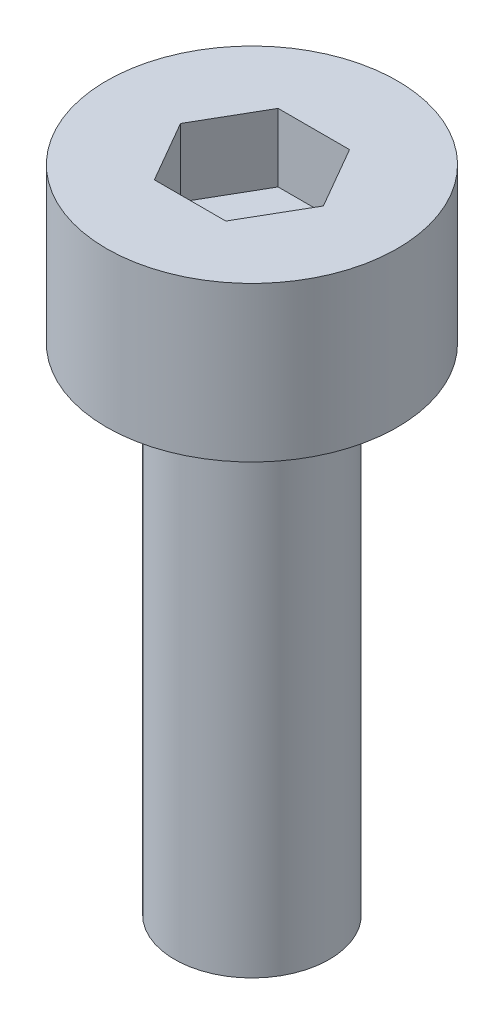
SolidWorks part; units mm, degrees
material "AISI 304"
ref_plane "前视基准面" through (0, 0, 0) normal (0, 0, 1) x (1, 0, 0)
ref_plane "上视基准面" through (0, 0, 0) normal (0, 1, 0) x (1, 0, 0)
ref_plane "右视基准面" through (0, 0, 0) normal (1, 0, 0) x (0, 0, -1)
sketch "草图1" plane through (0, 0, 0) normal (0, 1, 0) x (1, 0, 0)
  circle A0 centre (0, 0) radius 2.35
  dimension "D1" = 4.7
extrude "杯头" add sketch "草图1" along normal blind 2.5
sketch "草图2" plane through (0, 2.5, 0) normal (0, 1, 0) x (1, 0, 0)
  line L1 (1.1547, 0) -> (0.5774, 1)
  line L2 (0.5774, 1) -> (-0.5774, 1)
  line L3 (-0.5774, 1) -> (-1.1547, 0)
  line L4 (-1.1547, 0) -> (-0.5774, -1)
  line L5 (-0.5774, -1) -> (0.5774, -1)
  line L6 (0.5774, -1) -> (1.1547, 0)
  circle A0 centre (0, 0) radius 1 construction
  dimension "D1" = 2
extrude "内六角口" cut sketch "草图2" against normal blind 1.1
sketch "草图3" plane through (0, 0, 0) normal (0, -1, 0) x (1, 0, 0)
  circle A0 centre (0, 0) radius 1.25
  dimension "D1" = 2.5
extrude "螺纹长" add sketch "草图3" along normal blind 8
